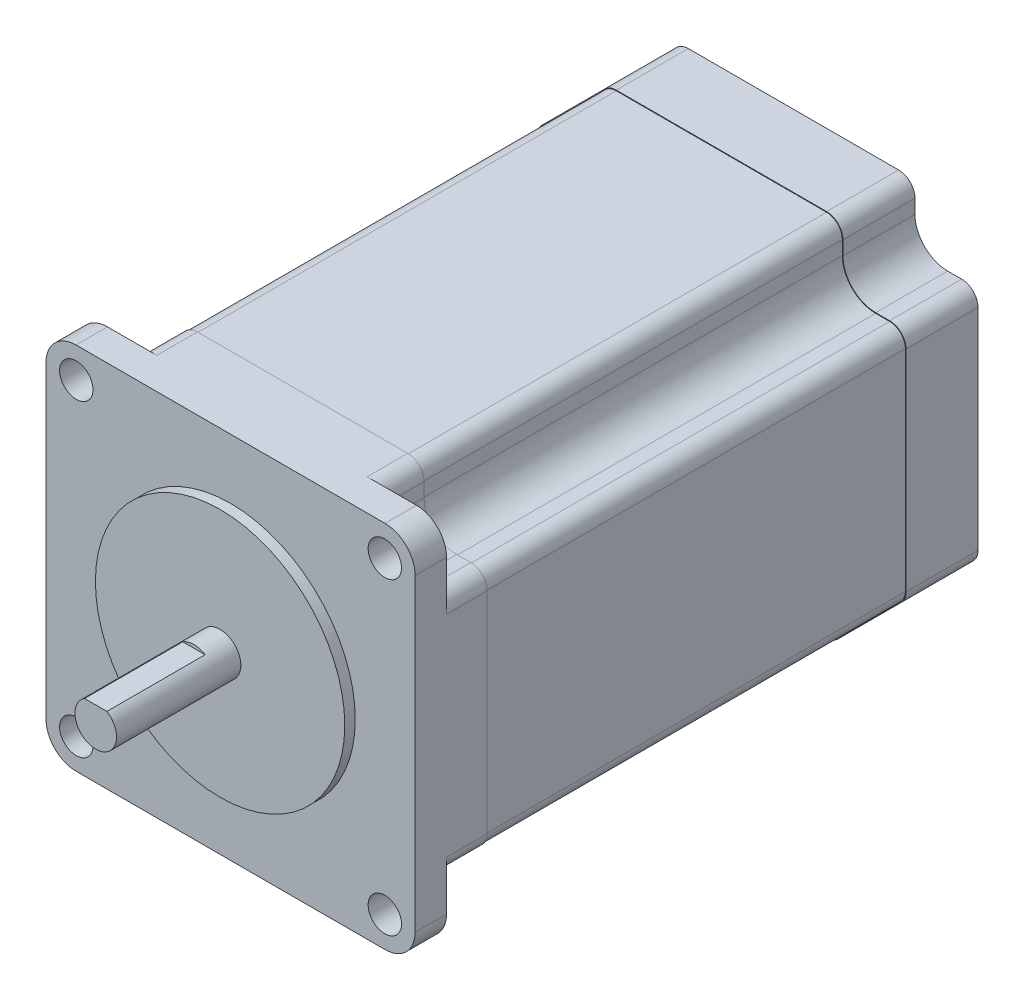
SolidWorks part; units mm, degrees
material "Plain Carbon Steel"
ref_plane "Front" through (0, 0, 0) normal (0, 0, 1) x (1, 0, 0)
ref_plane "Top" through (0, 0, 0) normal (0, 1, 0) x (1, 0, 0)
ref_plane "Right" through (0, 0, 0) normal (1, 0, 0) x (0, 0, -1)
sketch "Sketch1" plane through (0, 0, 0) normal (0, 0, 1) x (1, 0, 0)
  circle A0 centre (0, 0) radius 3.175
  dimension "D1" = 6.35
extrude "Boss-Extrude1" add sketch "Sketch1" along normal blind 20.6
sketch "Sketch2" plane through (0, 0, 0) normal (0, 0, -1) x (-1, 0, 0)
  circle A0 centre (0, 0) radius 19.05
  dimension "D1" = 38.1
extrude "Boss-Extrude2" add sketch "Sketch2" against normal blind 1.6
sketch "Sketch3" plane through (0, 0, 0) normal (0, 0, -1) x (-1, 0, 0)
  line L1 (23.6, -28.2) -> (-23.6, -28.2)
  line L2 (28.2, -23.6) -> (28.2, 23.6)
  line L3 (23.6, 28.2) -> (-23.6, 28.2)
  line L4 (-28.2, -23.6) -> (-28.2, 23.6)
  line L5 (28.2, -28.2) -> (-28.2, 28.2) construction
  line L6 (28.2, 28.2) -> (-28.2, -28.2) construction
  arc A0 (28.2, 23.6) -> (23.6, 28.2) centre (23.6, 23.6) ccw
  arc A1 (23.6, -28.2) -> (28.2, -23.6) centre (23.6, -23.6) ccw
  arc A2 (-23.6, -28.2) -> (-28.2, -23.6) centre (-23.6, -23.6) cw
  arc A3 (-23.6, 28.2) -> (-28.2, 23.6) centre (-23.6, 23.6) ccw
  point P0 (0, 0)
  dimension "D2" = 4.6
  dimension "D1" = 56.4
extrude "Boss-Extrude3" add sketch "Sketch3" along normal blind 4.8
sketch "Sketch4" plane through (0, 0, -4.8) normal (0, 0, -1) x (-1, 0, 0)
  line L0 (-12.9329, 0) -> (0, 0) construction
  line L1 (0, 0) -> (0, 12.5926) construction
  line L2 (-18.57, 23.57) -> (-18.57, 25.7)
  line L4 (28.2, 16.07) -> (28.2, -16.07)
  line L5 (-23.57, 18.57) -> (-25.7, 18.57)
  line L6 (16.07, 28.2) -> (-16.07, 28.2)
  line L7 (-28.2, 23.6) -> (-28.2, -23.6) construction
  line L8 (-28.2, 16.07) -> (-28.2, -16.07)
  line L9 (23.6, 28.2) -> (-23.6, 28.2) construction
  line L10 (23.57, 18.57) -> (25.7, 18.57)
  line L12 (18.57, 23.57) -> (18.57, 25.7)
  line L13 (18.57, -23.57) -> (18.57, -25.7)
  line L15 (23.57, -18.57) -> (25.7, -18.57)
  line L16 (16.07, -28.2) -> (-16.07, -28.2)
  line L17 (-23.57, -18.57) -> (-25.7, -18.57)
  line L19 (-18.57, -23.57) -> (-18.57, -25.7)
  arc A0 (-18.57, 25.7) -> (-16.07, 28.2) centre (-16.07, 25.7) cw
  arc A1 (-23.57, 18.57) -> (-18.57, 23.57) centre (-23.57, 23.57) ccw
  arc A2 (-25.7, 18.57) -> (-28.2, 16.07) centre (-25.7, 16.07) ccw
  arc A3 (25.7, 18.57) -> (28.2, 16.07) centre (25.7, 16.07) cw
  arc A4 (23.57, 18.57) -> (18.57, 23.57) centre (23.57, 23.57) cw
  arc A5 (18.57, 25.7) -> (16.07, 28.2) centre (16.07, 25.7) ccw
  arc A6 (18.57, -25.7) -> (16.07, -28.2) centre (16.07, -25.7) cw
  arc A7 (23.57, -18.57) -> (18.57, -23.57) centre (23.57, -23.57) ccw
  arc A8 (25.7, -18.57) -> (28.2, -16.07) centre (25.7, -16.07) ccw
  arc A9 (-25.7, -18.57) -> (-28.2, -16.07) centre (-25.7, -16.07) cw
  arc A10 (-23.57, -18.57) -> (-18.57, -23.57) centre (-23.57, -23.57) cw
  arc A11 (-18.57, -25.7) -> (-16.07, -28.2) centre (-16.07, -25.7) ccw
  point P16 (28.2, 0)
  point P27 (0, 28.2)
  point P49 (0, -28.2)
  point P51 (-28.2, 0)
  dimension "D2" = 47.14
  dimension "D3" = 2.5
  dimension "4.6*2" = 10
  dimension "D4" = 47.14
extrude "Boss-Extrude4" add sketch "Sketch4" along normal blind 81.2
sketch "Sketch7" plane through (0, 0, 20.6) normal (0, 0, 1) x (1, 0, 0)
  line L1 (-1.7103, 2.675) -> (1.7103, 2.675)
  line L2 (-1.7103, 2.675) -> (-1.7103, 3.7877)
  line L3 (-1.7103, 3.7877) -> (1.7103, 3.7877)
  line L4 (1.7103, 2.675) -> (1.7103, 3.7877)
  circle A0 centre (0, 0) radius 3.175 construction
  dimension "D1" = 5.85
extrude "Cut-Extrude5" cut sketch "Sketch7" against normal blind 15
sketch "Sketch8" plane through (0, 0, 0) normal (0, 0, 1) x (1, 0, 0)
  line L0 (-13.3219, 0) -> (0, 0) construction
  line L1 (0, 0) -> (0, 15.3153) construction
  circle A0 centre (-23.57, 23.57) radius 2.55
  circle A1 centre (23.57, 23.57) radius 2.55
  circle A2 centre (23.57, -23.57) radius 2.55
  circle A3 centre (-23.57, -23.57) radius 2.55
  dimension "D2" = 47.14
  dimension "D3" = 5.1
  dimension "D1" = 47.14
extrude "Cut-Extrude6" cut sketch "Sketch8" against normal up to next
ref_plane "Plane1" through (0, 0, -43) normal (0, 0, 1) x (1, 0, 0)
sketch "Sketch9" plane through (0, 0, -43) normal (0, 0, 1) x (1, 0, 0)
  line L24 (18.47, 23.57) -> (18.47, 25.7)
  line L25 (25.7, 18.47) -> (23.57, 18.47)
  line L26 (28.1, -16.07) -> (28.1, 16.07)
  line L27 (23.57, -18.47) -> (25.7, -18.47)
  line L28 (18.47, -25.7) -> (18.47, -23.57)
  line L29 (-16.07, -28.1) -> (16.07, -28.1)
  line L30 (-18.47, -23.57) -> (-18.47, -25.7)
  line L31 (-25.7, -18.47) -> (-23.57, -18.47)
  line L32 (-28.1, 16.07) -> (-28.1, -16.07)
  line L33 (-23.57, 18.47) -> (-25.7, 18.47)
  line L34 (-18.47, 25.7) -> (-18.47, 23.57)
  line L35 (16.07, 28.1) -> (-16.07, 28.1)
  line L36 (18.47, 23.57) -> (18.47, 25.7)
  line L37 (25.7, 18.47) -> (23.57, 18.47)
  line L38 (28.1, -16.07) -> (28.1, 16.07)
  line L39 (23.57, -18.47) -> (25.7, -18.47)
  line L40 (18.47, -25.7) -> (18.47, -23.57)
  line L41 (-16.07, -28.1) -> (16.07, -28.1)
  line L42 (-18.47, -23.57) -> (-18.47, -25.7)
  line L43 (-25.7, -18.47) -> (-23.57, -18.47)
  line L44 (-28.1, 16.07) -> (-28.1, -16.07)
  line L45 (-23.57, 18.47) -> (-25.7, 18.47)
  line L46 (-18.47, 25.7) -> (-18.47, 23.57)
  line L47 (16.07, 28.1) -> (-16.07, 28.1)
  line L48 (18.57, 23.57) -> (18.57, 25.7)
  line L49 (25.7, 18.57) -> (23.57, 18.57)
  line L50 (28.2, -16.07) -> (28.2, 16.07)
  line L51 (23.57, -18.57) -> (25.7, -18.57)
  line L52 (18.57, -25.7) -> (18.57, -23.57)
  line L53 (-16.07, -28.2) -> (16.07, -28.2)
  line L54 (-18.57, -23.57) -> (-18.57, -25.7)
  line L55 (-25.7, -18.57) -> (-23.57, -18.57)
  line L56 (-28.2, 16.07) -> (-28.2, -16.07)
  line L57 (-23.57, 18.57) -> (-25.7, 18.57)
  line L58 (-18.57, 25.7) -> (-18.57, 23.57)
  line L59 (16.07, 28.2) -> (-16.07, 28.2)
  line L60 (18.57, 23.57) -> (18.57, 25.7)
  line L61 (25.7, 18.57) -> (23.57, 18.57)
  line L62 (28.2, -16.07) -> (28.2, 16.07)
  line L63 (23.57, -18.57) -> (25.7, -18.57)
  line L64 (18.57, -25.7) -> (18.57, -23.57)
  line L65 (-16.07, -28.2) -> (16.07, -28.2)
  line L66 (-18.57, -23.57) -> (-18.57, -25.7)
  line L67 (-25.7, -18.57) -> (-23.57, -18.57)
  line L68 (-28.2, 16.07) -> (-28.2, -16.07)
  line L69 (-23.57, 18.57) -> (-25.7, 18.57)
  line L70 (-18.57, 25.7) -> (-18.57, 23.57)
  line L71 (16.07, 28.2) -> (-16.07, 28.2)
  arc A24 (18.47, 25.7) -> (16.07, 28.1) centre (16.07, 25.7) ccw
  arc A25 (18.47, 23.57) -> (23.57, 18.47) centre (23.57, 23.57) ccw
  arc A26 (28.1, 16.07) -> (25.7, 18.47) centre (25.7, 16.07) ccw
  arc A27 (25.7, -18.47) -> (28.1, -16.07) centre (25.7, -16.07) ccw
  arc A28 (23.57, -18.47) -> (18.47, -23.57) centre (23.57, -23.57) ccw
  arc A29 (16.07, -28.1) -> (18.47, -25.7) centre (16.07, -25.7) ccw
  arc A30 (-18.47, -25.7) -> (-16.07, -28.1) centre (-16.07, -25.7) ccw
  arc A31 (-18.47, -23.57) -> (-23.57, -18.47) centre (-23.57, -23.57) ccw
  arc A32 (-28.1, -16.07) -> (-25.7, -18.47) centre (-25.7, -16.07) ccw
  arc A33 (-25.7, 18.47) -> (-28.1, 16.07) centre (-25.7, 16.07) ccw
  arc A34 (-23.57, 18.47) -> (-18.47, 23.57) centre (-23.57, 23.57) ccw
  arc A35 (-16.07, 28.1) -> (-18.47, 25.7) centre (-16.07, 25.7) ccw
  arc A36 (18.47, 25.7) -> (16.07, 28.1) centre (16.07, 25.7) ccw
  arc A37 (18.47, 23.57) -> (23.57, 18.47) centre (23.57, 23.57) ccw
  arc A38 (28.1, 16.07) -> (25.7, 18.47) centre (25.7, 16.07) ccw
  arc A39 (25.7, -18.47) -> (28.1, -16.07) centre (25.7, -16.07) ccw
  arc A40 (23.57, -18.47) -> (18.47, -23.57) centre (23.57, -23.57) ccw
  arc A41 (16.07, -28.1) -> (18.47, -25.7) centre (16.07, -25.7) ccw
  arc A42 (-18.47, -25.7) -> (-16.07, -28.1) centre (-16.07, -25.7) ccw
  arc A43 (-18.47, -23.57) -> (-23.57, -18.47) centre (-23.57, -23.57) ccw
  arc A44 (-28.1, -16.07) -> (-25.7, -18.47) centre (-25.7, -16.07) ccw
  arc A45 (-25.7, 18.47) -> (-28.1, 16.07) centre (-25.7, 16.07) ccw
  arc A46 (-23.57, 18.47) -> (-18.47, 23.57) centre (-23.57, 23.57) ccw
  arc A47 (-16.07, 28.1) -> (-18.47, 25.7) centre (-16.07, 25.7) ccw
  arc A48 (18.57, 25.7) -> (16.07, 28.2) centre (16.07, 25.7) ccw
  arc A49 (18.57, 23.57) -> (23.57, 18.57) centre (23.57, 23.57) ccw
  arc A50 (28.2, 16.07) -> (25.7, 18.57) centre (25.7, 16.07) ccw
  arc A51 (25.7, -18.57) -> (28.2, -16.07) centre (25.7, -16.07) ccw
  arc A52 (23.57, -18.57) -> (18.57, -23.57) centre (23.57, -23.57) ccw
  arc A53 (16.07, -28.2) -> (18.57, -25.7) centre (16.07, -25.7) ccw
  arc A54 (-18.57, -25.7) -> (-16.07, -28.2) centre (-16.07, -25.7) ccw
  arc A55 (-18.57, -23.57) -> (-23.57, -18.57) centre (-23.57, -23.57) ccw
  arc A56 (-28.2, -16.07) -> (-25.7, -18.57) centre (-25.7, -16.07) ccw
  arc A57 (-25.7, 18.57) -> (-28.2, 16.07) centre (-25.7, 16.07) ccw
  arc A58 (-23.57, 18.57) -> (-18.57, 23.57) centre (-23.57, 23.57) ccw
  arc A59 (-16.07, 28.2) -> (-18.57, 25.7) centre (-16.07, 25.7) ccw
  arc A60 (18.57, 25.7) -> (16.07, 28.2) centre (16.07, 25.7) ccw
  arc A61 (18.57, 23.57) -> (23.57, 18.57) centre (23.57, 23.57) ccw
  arc A62 (28.2, 16.07) -> (25.7, 18.57) centre (25.7, 16.07) ccw
  arc A63 (25.7, -18.57) -> (28.2, -16.07) centre (25.7, -16.07) ccw
  arc A64 (23.57, -18.57) -> (18.57, -23.57) centre (23.57, -23.57) ccw
  arc A65 (16.07, -28.2) -> (18.57, -25.7) centre (16.07, -25.7) ccw
  arc A66 (-18.57, -25.7) -> (-16.07, -28.2) centre (-16.07, -25.7) ccw
  arc A67 (-18.57, -23.57) -> (-23.57, -18.57) centre (-23.57, -23.57) ccw
  arc A68 (-28.2, -16.07) -> (-25.7, -18.57) centre (-25.7, -16.07) ccw
  arc A69 (-25.7, 18.57) -> (-28.2, 16.07) centre (-25.7, 16.07) ccw
  arc A70 (-23.57, 18.57) -> (-18.57, 23.57) centre (-23.57, 23.57) ccw
  arc A71 (-16.07, 28.2) -> (-18.57, 25.7) centre (-16.07, 25.7) ccw
  dimension "D1" = 0.1
  dimension "D2" = 0
extrude "Cut-Extrude7" cut sketch "Sketch9" against normal mid plane 64
